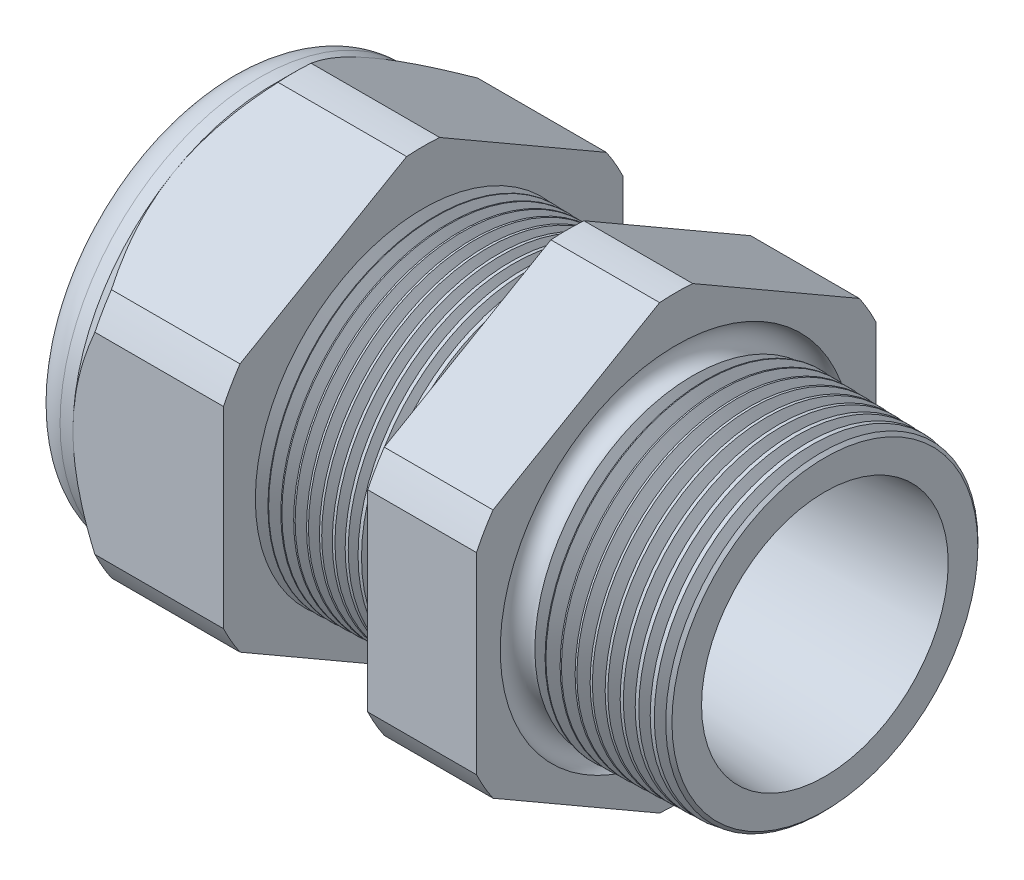
SolidWorks part; units mm, degrees
ref_plane "Front Plane" through (0, 0, 0) normal (0, 0, 1) x (1, 0, 0)
ref_plane "Top Plane" through (0, 0, 0) normal (0, 1, 0) x (1, 0, 0)
ref_plane "Right Plane" through (0, 0, 0) normal (1, 0, 0) x (0, 0, -1)
sketch "Sketch10" plane through (0, 0, 0) normal (0, 0, 1) x (1, 0, 0)
  line L0 (0, 0) -> (-115.3565, 0) construction
  line L1 (-34.798, 5.969) -> (-22.998, 5.969)
  line L2 (1.016, 7.3722) -> (1.016, 9.4042)
  line L3 (-7.874, 9.637) -> (1.016, 9.4042)
  line L4 (-7.874, 23.876) -> (-7.874, 9.637)
  line L5 (-7.874, 23.876) -> (-14.374, 23.876)
  line L6 (-14.374, 23.876) -> (-14.374, 9.8072)
  line L7 (-22.998, 10.033) -> (-14.374, 9.8072)
  line L8 (-22.998, 10.033) -> (-22.998, 23.876)
  line L9 (-22.998, 23.876) -> (-31.998, 23.876)
  line L10 (-31.998, 23.876) -> (-31.998, 11.938)
  line L11 (-31.998, 11.938) -> (-34.798, 11.938)
  line L12 (-34.798, 11.938) -> (-34.798, 5.969)
  line L13 (-22.998, 5.969) -> (1.016, 7.3722)
  dimension "D1" = 35.814
  dimension "D2" = 11.938
  dimension "D3" = 1.5
  dimension "D4" = 2.032
  dimension "A" = 20.066
  dimension "D6" = 23.876
  dimension "D8" = 47.752
  dimension "D9" = 2.8
  dimension "D10" = 9
  dimension "D11" = 6.5
  dimension "D" = 8.89
revolve "Revolve2" add sketch "Sketch10" angle 360 about L0
sketch "Sketch12" plane through (-31.998, 0, 0) normal (-1, 0, 0) x (0, 0, 1)
  line L1 (-0.9882, 13.2143) -> (-10.9498, 7.4629)
  line L2 (-11.938, 5.7513) -> (-11.938, -5.7513)
  line L3 (-10.9498, -7.4629) -> (-0.9882, -13.2143)
  line L4 (0.9882, -13.2143) -> (10.9498, -7.4629)
  line L5 (11.938, -5.7513) -> (11.938, 5.7513)
  line L6 (10.9498, 7.4629) -> (0.9882, 13.2143)
  circle A0 centre (0, 0) radius 11.938 construction
  arc A1 (0.9882, 13.2143) -> (-0.9882, 13.2143) centre (0, 0) ccw
  arc A2 (-10.9498, 7.4629) -> (-11.938, 5.7513) centre (0, 0) ccw
  arc A3 (-11.938, -5.7513) -> (-10.9498, -7.4629) centre (0, 0) ccw
  arc A4 (-0.9882, -13.2143) -> (0.9882, -13.2143) centre (0, 0) ccw
  arc A5 (10.9498, -7.4629) -> (11.938, -5.7513) centre (0, 0) ccw
  arc A6 (11.938, 5.7513) -> (10.9498, 7.4629) centre (0, 0) ccw
  dimension "D2" = 26.5024
  dimension "D1" = 23.876
extrude "Cut-Extrude2" cut sketch "Sketch12" against normal through all flip side to cut
fillet "Fillet4" radius 2.032 1 edges at (-34.798, 0, -11.938)
sketch "Sketch19" plane through (-31.998, 0, 0) normal (-1, 0, 0) x (0, 0, 1)
  line L0 (11.938, 0) -> (11.938, 5.7513) construction
  circle A0 centre (0, 0) radius 11.938
extrude "Cut-Extrude3" cut sketch "Sketch19" against normal blind 2 draft 45 flip side to cut
chamfer "Chamfer1" distance 0.254 angle 45 1 edges at (1.016, 0, -9.4042)
sketch "Sketch21" plane through (-34.798, 0, 0) normal (-1, 0, 0) x (0, 0, 1)
  circle A0 centre (0, 0) radius 5.969
  circle A2 centre (0, 0) radius 5.969 construction
extrude "plug" add sketch "Sketch21" against normal blind 6.35 separate body
sketch "Sketch22" plane through (-34.798, 0, 0) normal (-1, 0, 0) x (0, 0, 1)
  circle A0 centre (0, 0) radius 5.715
  circle A1 centre (0, 0) radius 5.969 construction
  dimension "D1" = 0.254
extrude "Cut-Extrude4" cut sketch "Sketch22" against normal blind 0.508
sketch "Sketch27" plane through (-34.29, 0, 0) normal (-1, 0, 0) x (0, 0, 1)
  line L0 (-4.3624, 0) -> (4.3624, 0) construction
  circle A0 centre (-3.1648, 0) radius 2.54
  circle A1 centre (0, 0) radius 5.715 construction
  dimension "D1" = 0.0102
  dimension "holedia" = 5.08
extrude "plugholes" cut sketch "Sketch27" against normal through all
pattern_circular "CirPattern1" count 2 over 360 about axis through (0, 0, 0) along (1, 0, 0) of "plugholes"
sketch "Sketch28" [suppressed] plane through (-29.464, 0, 0) normal (-1, 0, 0) x (0, 0, 1)
  circle A0 centre (0, 0) radius 0.762
  dimension "midholedia" = 5.08
extrude "midhole" [suppressed] cut sketch "Sketch28" against normal through all
sketch "Sketch29" plane through (0, 0, 0) normal (0, 0, 1) x (1, 0, 0)
  line L0 (-22.998, 10.033) -> (-22.265, 10.0138)
  line L1 (-14.374, 9.8072) -> (-22.998, 10.033) construction
  line L2 (-22.265, 10.0138) -> (-22.6481, 9.3886)
  line L3 (-22.6481, 9.3886) -> (-22.998, 10.033)
  dimension "D1" = 60
  dimension "D2" = 60
  dimension "D3" = 0.635
revolve "Cut-Revolve1" cut sketch "Sketch29" angle 360 about axis through (0, 0, 0) along (-1, 0, 0)
pattern_linear "LPattern1" count 11 spacing 0.762 along (1, 0, 0) of "Cut-Revolve1"
sketch "Sketch30" plane through (0, 0, 0) normal (0, 0, 1) x (1, 0, 0)
  line L0 (-7.874, 9.637) -> (-6.9944, 9.6139)
  line L1 (-7.874, 13.2143) -> (-7.874, 7.4629) construction
  line L2 (0.7621, 9.4108) -> (-7.874, 9.637) construction
  line L3 (-6.9944, 9.6139) -> (-7.4542, 8.8637)
  line L4 (-7.4542, 8.8637) -> (-7.874, 9.637)
  dimension "D1" = 60
  dimension "D2" = 60
  dimension "D3" = 0.762
revolve "Cut-Revolve2" cut sketch "Sketch30" angle 360 about axis through (0, 0, 0) along (-1, 0, 0)
pattern_linear "LPattern2" count 10 spacing 0.889 along (1, 0, 0) of "Cut-Revolve2"
sketch "Sketch31" [suppressed] plane through (-38.354, 0, 0) normal (-1, 0, 0) x (0, 0, 1)
  line L0 (-1.905, 1.905) -> (1.905, 1.905)
  line L1 (-1.905, -1.905) -> (1.905, -1.905)
  circle A0 centre (0, 0) radius 1.905 construction
  arc A1 (-1.905, 1.905) -> (-1.905, -1.905) centre (-1.905, 0) ccw
  arc A2 (1.905, 1.905) -> (1.905, -1.905) centre (1.905, 0) cw
extrude "Cut-Extrude5" [suppressed] cut sketch "Sketch31" against normal through all
sketch "Sketch32" plane through (0, 0, 0) normal (0, 0, 1) x (1, 0, 0)
  line L0 (-7.874, 13.2143) -> (-7.874, 7.4629) construction
  circle A0 centre (-7.747, 9.637) radius 0.889
  dimension "D2" = 1.778
  dimension "D1" = 0.127
revolve "Cut-Revolve3" cut sketch "Sketch32" angle 360 about axis through (0, 0, 0) along (-1, 0, 0)
